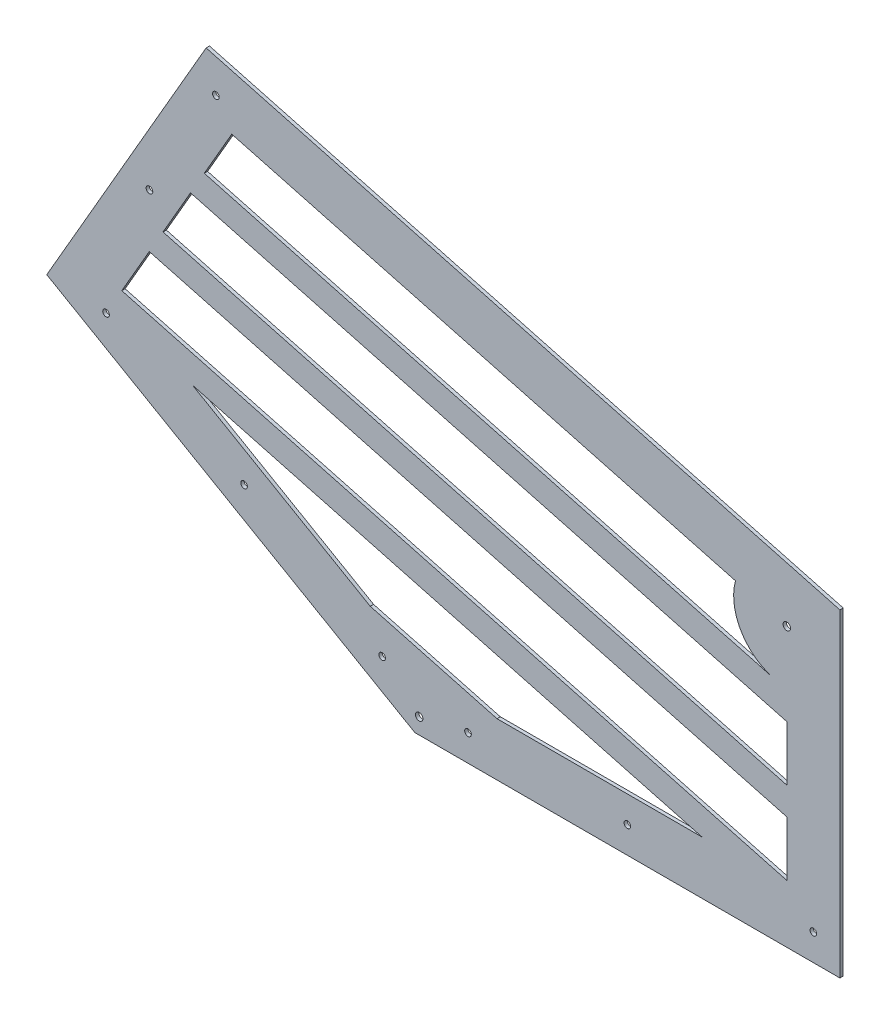
SolidWorks part; units mm, degrees
ref_plane "정면" through (0, 0, 0) normal (0, 0, 1) x (1, 0, 0)
ref_plane "윗면" through (0, 0, 0) normal (0, 1, 0) x (1, 0, 0)
ref_plane "우측면" through (0, 0, 0) normal (1, 0, 0) x (0, 0, -1)
sketch "스케치1" plane through (0, 0, 0) normal (0, 0, 1) x (1, 0, 0)
  line L5 (0, 0) -> (203.2, 0)
  line L9 (203.2, 0) -> (203.2, 152.4)
  line L12 (203.2, 152.4) -> (-99.7764, 233.5823)
  line L13 (0, 0) -> (-175.9764, 101.6)
  line L16 (-175.9764, 101.6) -> (-99.7764, 233.5823)
  line L18 (-106.3015, 90.7026) -> (-21.3114, 41.6336)
  line L19 (39.273, 25.4) -> (137.4111, 25.4)
  line L20 (177.8, 27.7258) -> (177.8, 54.0218)
  line L22 (-100.6724, 181.2303) -> (171.226, 108.3754)
  line L23 (-107.2464, 169.8438) -> (177.8, 93.4659)
  line L24 (177.8, 67.1699) -> (-120.3944, 147.0708)
  line L25 (-126.9684, 135.6843) -> (177.8, 54.0218)
  line L26 (177.8, 27.7258) -> (-140.1164, 112.9113)
  line L27 (-106.3015, 90.7026) -> (137.4111, 25.4)
  line L28 (39.273, 25.4) -> (-21.3114, 41.6336)
  line L29 (177.8, 67.1699) -> (177.8, 93.4659)
  line L30 (-126.9684, 135.6843) -> (-140.1164, 112.9113)
  line L31 (-107.2464, 169.8438) -> (-120.3944, 147.0708)
  line L33 (-87.5244, 204.0033) -> (-100.6724, 181.2303)
  line L35 (153.2655, 139.4839) -> (-87.5244, 204.0033)
  circle A0 centre (2.0418, 7.62) radius 1.7859
  circle A1 centre (177.8, 132.9099) radius 1.7859
  circle A2 centre (190.5, 12.7) radius 1.5875
  circle A3 centre (101.6, 12.7) radius 1.5875
  circle A4 centre (25.4, 12.7) radius 1.5875
  circle A5 centre (-147.6293, 99.8985) radius 1.5875
  circle A6 centre (-81.6382, 61.7985) radius 1.5875
  circle A7 centre (-15.647, 23.6985) radius 1.5875
  circle A8 centre (-95.1278, 216.2337) radius 1.5875
  circle A9 centre (-126.8778, 161.2411) radius 1.5875
  arc A10 (153.2655, 139.4839) -> (171.226, 108.3754) centre (177.8, 132.9099) ccw
  dimension "D3" = 152.4
  dimension "D4" = 152.4
  dimension "D10" = 3.5719
  dimension "D13" = 25.4
  dimension "D15" = 3.5719
  dimension "D16" = 25.4
  dimension "D28" = 3.175
  dimension "D29" = 3.175
  dimension "D30" = 3.175
  dimension "D31" = 3.175
  dimension "D32" = 3.175
  dimension "D33" = 3.175
  dimension "D34" = 12.7
  dimension "D36" = 3.175
  dimension "D37" = 3.175
  dimension "D1" = 203.2
  dimension "D2" = 203.2
  dimension "D5" = 90
  dimension "D6" = 90
  dimension "D7" = 150
  dimension "D8" = 105
  dimension "D9" = 105
  dimension "D11" = 7.62
  dimension "D12" = 7.62
  dimension "D14" = 25.4
  dimension "D17" = 101.6
  dimension "D18" = 177.8
  dimension "D19" = 177.8
  dimension "D20" = 101.6
  dimension "D21" = 12.7
  dimension "D22" = 12.7
  dimension "D23" = 12.7
  dimension "D24" = 12.7
  dimension "D25" = 12.7
  dimension "D26" = 12.7
  dimension "D27" = 12.7
  dimension "D35" = 12.7
  dimension "D38" = 76.2
  dimension "D39" = 139.7
  dimension "D42" = 25.4
  dimension "D43" = 25.4
  dimension "D44" = 25.4
  dimension "D46" = 12.7
  dimension "D47" = 25.4
  dimension "D48" = 12.7
  dimension "D49" = 25.4
  dimension "D50" = 12.7
  dimension "D51" = 25.4
extrude "보스-돌출1" add sketch "스케치1" along normal blind 1.5875
